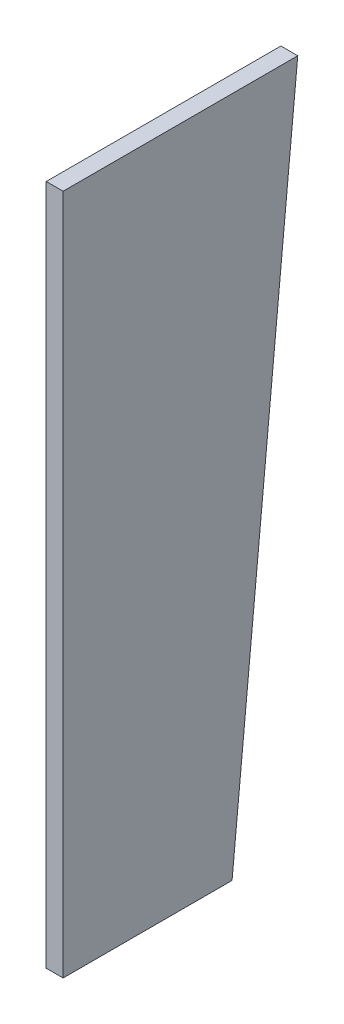
SolidWorks part; units mm, degrees
ref_plane "Front Plane" through (0, 0, 0) normal (0, 0, 1) x (1, 0, 0)
ref_plane "Top Plane" through (0, 0, 0) normal (0, 1, 0) x (1, 0, 0)
ref_plane "Right Plane" through (0, 0, 0) normal (1, 0, 0) x (0, 0, -1)
sketch "Sketch1" plane through (0, 0, 0) normal (1, 0, 0) x (0, 0, -1)
  line L0 (0, 0) -> (0, 726)
  line L1 (0, 726) -> (250, 726)
  line L2 (250, 726) -> (180, 0)
  line L3 (180, 0) -> (0, 0)
  dimension "D1" = 726
  dimension "D2" = 250
  dimension "D3" = 180
extrude "Boss-Extrude1" add sketch "Sketch1" along normal blind 18
